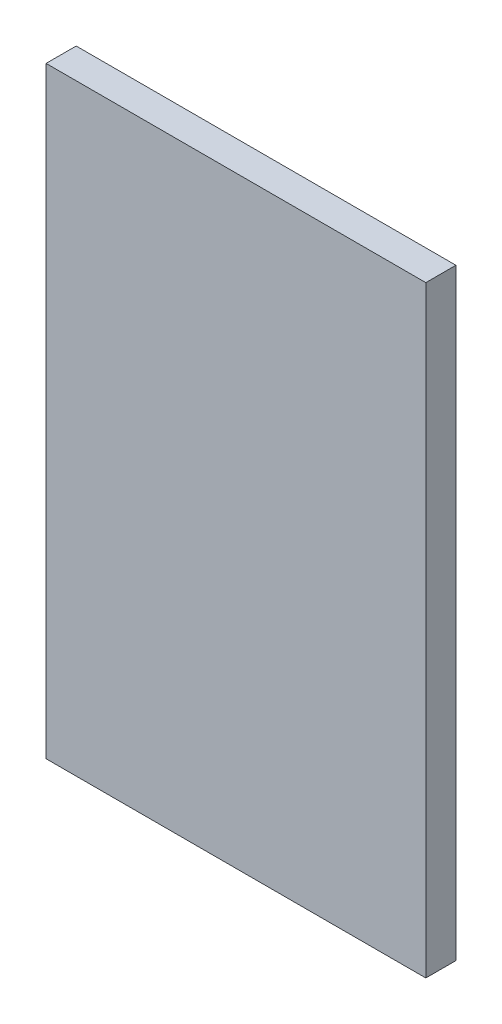
SolidWorks part; units mm, degrees
ref_plane "Front Plane" through (0, 0, 0) normal (0, 0, 1) x (1, 0, 0)
ref_plane "Top Plane" through (0, 0, 0) normal (0, 1, 0) x (1, 0, 0)
ref_plane "Right Plane" through (0, 0, 0) normal (1, 0, 0) x (0, 0, -1)
sketch "Sketch1" plane through (0, 0, 0) normal (0, 0, 1) x (1, 0, 0)
  line L1 (0, 0) -> (560.57, 0)
  line L2 (0, 0) -> (0, -889)
  line L3 (0, -889) -> (560.57, -889)
  line L4 (560.57, 0) -> (560.57, -889)
  dimension "D1" = 889
  dimension "D2" = 560.57
extrude "Boss-Extrude1" add sketch "Sketch1" along normal blind 44.45
ref_plane "Hinge Mirror Plane" through (0, -444.5, 0) normal (0, 1, 0) x (1, 0, 0)
sketch "Sketch2" plane through (0, -444.5, 0) normal (0, 1, 0) x (1, 0, 0)
  line L0 (75.4357, -10) -> (75.4357, 0)
  line L1 (560.57, 0) -> (0, 0) construction
  line L2 (75.4357, 0) -> (111.5643, 0)
  line L3 (111.5643, 0) -> (111.5643, -10)
  line L4 (0, -44.45) -> (0, 0) construction
  line L5 (168.9357, -10) -> (168.9357, 0)
  line L6 (168.9357, 0) -> (205.0643, 0)
  line L7 (205.0643, 0) -> (205.0643, -10)
  arc A0 (75.4357, -10) -> (111.5643, -10) centre (93.5, -3.9517) ccw
  arc A1 (168.9357, -10) -> (205.0643, -10) centre (187, -3.9517) ccw
  dimension "D1" = 19.05
  dimension "D7" = 19.05
  dimension "D2" = 36.1287
  dimension "D3" = 10
  dimension "D4" = 93.5
  dimension "D5" = 93.5
  dimension "D6" = 10
ref_plane "Plane2" through (280.285, 0, 0) normal (-1, 0, 0) x (0, 0, 1)
extrude "Cut-Extrude2" cut sketch "Sketch2" against normal blind 381 and the other way blind 381
mirror "Mirror1" about plane through (280.285, 0, 0) normal (-1, 0, 0) of "Cut-Extrude2"
